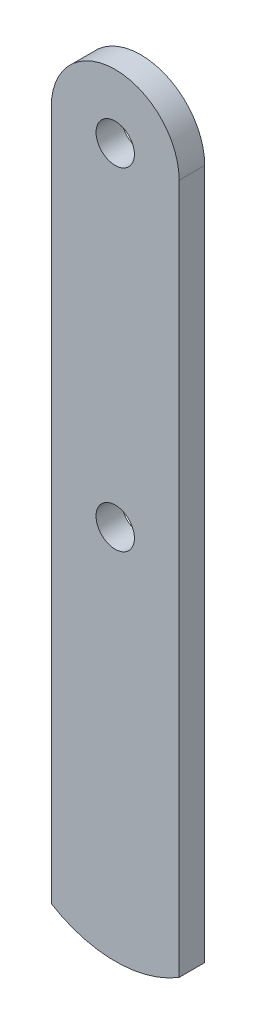
SolidWorks part; units mm, degrees
ref_plane "Front Plane" through (0, 0, 0) normal (0, 0, 1) x (1, 0, 0)
ref_plane "Top Plane" through (0, 0, 0) normal (0, 1, 0) x (1, 0, 0)
ref_plane "Right Plane" through (0, 0, 0) normal (1, 0, 0) x (0, 0, -1)
sketch "Sketch1" plane through (0, 0, 0) normal (0, 0, 1) x (1, 0, 0)
  line L0 (0, 24.5) -> (0, -30.5) construction
  line L2 (-5, 24.5) -> (-5, -29.5)
  line L4 (5, 24.5) -> (5, -29.5)
  line L5 (-5, 29.5) -> (5, -29.5) construction
  line L6 (-5, -29.5) -> (5, 29.5) construction
  circle A0 centre (0, 24.5) radius 1.5
  arc A1 (5, 24.5) -> (-5, 24.5) centre (0, 24.5) ccw
  circle A2 centre (0, -1.5) radius 1.5
  arc A3 (5, -29.5) -> (-5, -29.5) centre (0, -21.3648) cw
  point P0 (0, 0)
  dimension "D3" = 3
  dimension "D4" = 26
  dimension "D1" = 59
  dimension "D2" = 10
extrude "Boss-Extrude1" add sketch "Sketch1" along normal blind 2
